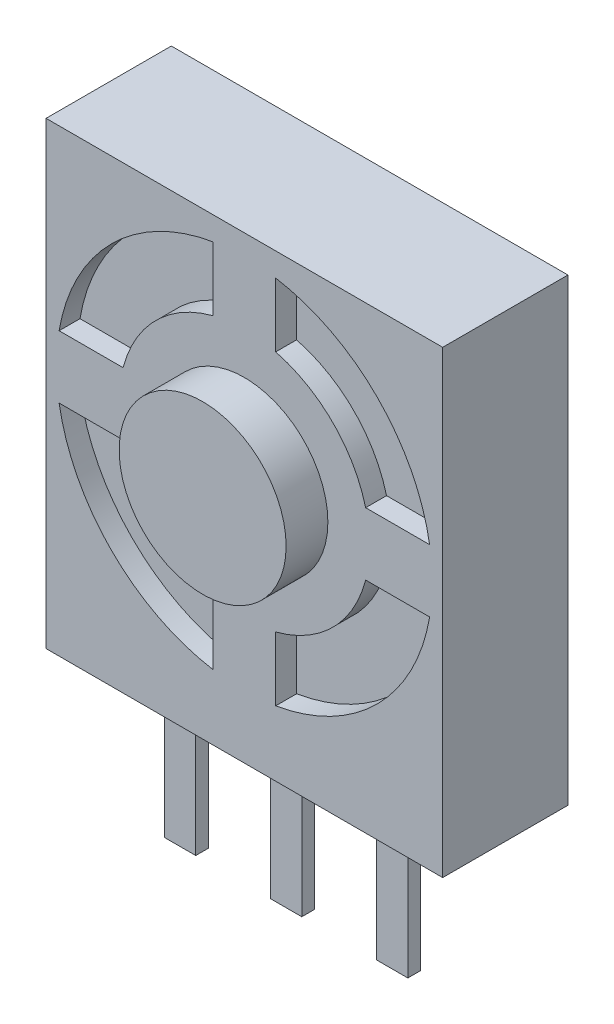
SolidWorks part; units mm, degrees
ref_plane "Plan de face" through (0, 0, 0) normal (0, 0, 1) x (1, 0, 0)
ref_plane "Plan de dessus" through (0, 0, 0) normal (0, 1, 0) x (1, 0, 0)
ref_plane "Plan de droite" through (0, 0, 0) normal (1, 0, 0) x (0, 0, -1)
sketch "Esquisse1" plane through (0, 0, 0) normal (0, 0, 1) x (1, 0, 0)
  line L1 (4.75, -5.5) -> (-4.75, -5.5)
  line L2 (4.75, -5.5) -> (4.75, 5.5)
  line L3 (4.75, 5.5) -> (-4.75, 5.5)
  line L4 (-4.75, -5.5) -> (-4.75, 5.5)
  line L5 (4.75, -5.5) -> (-4.75, 5.5) construction
  line L6 (4.75, 5.5) -> (-4.75, -5.5) construction
  point P0 (0, 0)
  dimension "D1" = 9.5
  dimension "D2" = 11
extrude "Boss.-Extru.1" add sketch "Esquisse1" along normal blind 3
sketch "Esquisse2" plane through (0, 0, 3) normal (0, 0, 1) x (1, 0, 0)
  line L0 (4.75, 5.5) -> (-4.75, 5.5) construction
  circle A0 centre (0, 0.5) radius 2
  dimension "D2" = 4
  dimension "D1" = 5
extrude "Boss.-Extru.2" add sketch "Esquisse2" along normal blind 1
sketch "Esquisse3" plane through (0, 0, 3) normal (0, 0, 1) x (1, 0, 0)
  line L0 (4.75, 5.5) -> (-4.75, 5.5) construction
  line L1 (5, 1.25) -> (-5, 1.25)
  line L2 (5, 1.25) -> (5, -0.25)
  line L3 (5, -0.25) -> (-5, -0.25)
  line L4 (-5, 1.25) -> (-5, -0.25)
  line L5 (5, 1.25) -> (-5, -0.25) construction
  line L6 (5, -0.25) -> (-5, 1.25) construction
  line L7 (-0.75, -4.5) -> (0.75, -4.5)
  line L8 (-0.75, -4.5) -> (-0.75, 5.5)
  line L9 (-0.75, 5.5) -> (0.75, 5.5)
  line L10 (0.75, -4.5) -> (0.75, 5.5)
  line L11 (-0.75, -4.5) -> (0.75, 5.5) construction
  line L12 (-0.75, 5.5) -> (0.75, -4.5) construction
  circle A0 centre (0, 0.5) radius 3
  circle A1 centre (0, 0.5) radius 4.5
  dimension "D1" = 6
  dimension "D2" = 9
  dimension "D3" = 1.5
extrude "Enlèv. mat.-Extru.1" cut sketch "Esquisse3" against normal blind 0.5 contours L8 A1 L1 A0 | L1 A1 L10 A0 | L10 A1 L3 A0 | L3 A1 L8 A0
sketch "Esquisse5" plane through (0, 0, 0) normal (1, 0, 0) x (0, 0, -1)
  line L0 (-3, -5.5) -> (0, -5.5) construction
  line L1 (-2, -5.5) -> (-1.7, -5.5)
  line L2 (-2, -5.5) -> (-2, -9)
  line L3 (-2, -9) -> (-1.7, -9)
  line L4 (-1.7, -5.5) -> (-1.7, -9)
  line L5 (-3, -5.5) -> (-3, 5.5) construction
  dimension "D1" = 3.5
  dimension "D2" = 0.3
  dimension "D3" = 1
extrude "Boss.-Extru.3" add sketch "Esquisse5" along normal mid plane 0.75 from offset 2.54 separate body
pattern_linear "Répétition linéaire1" count 3 spacing 2.54 along (-1, 0, 0) of bodies 104
